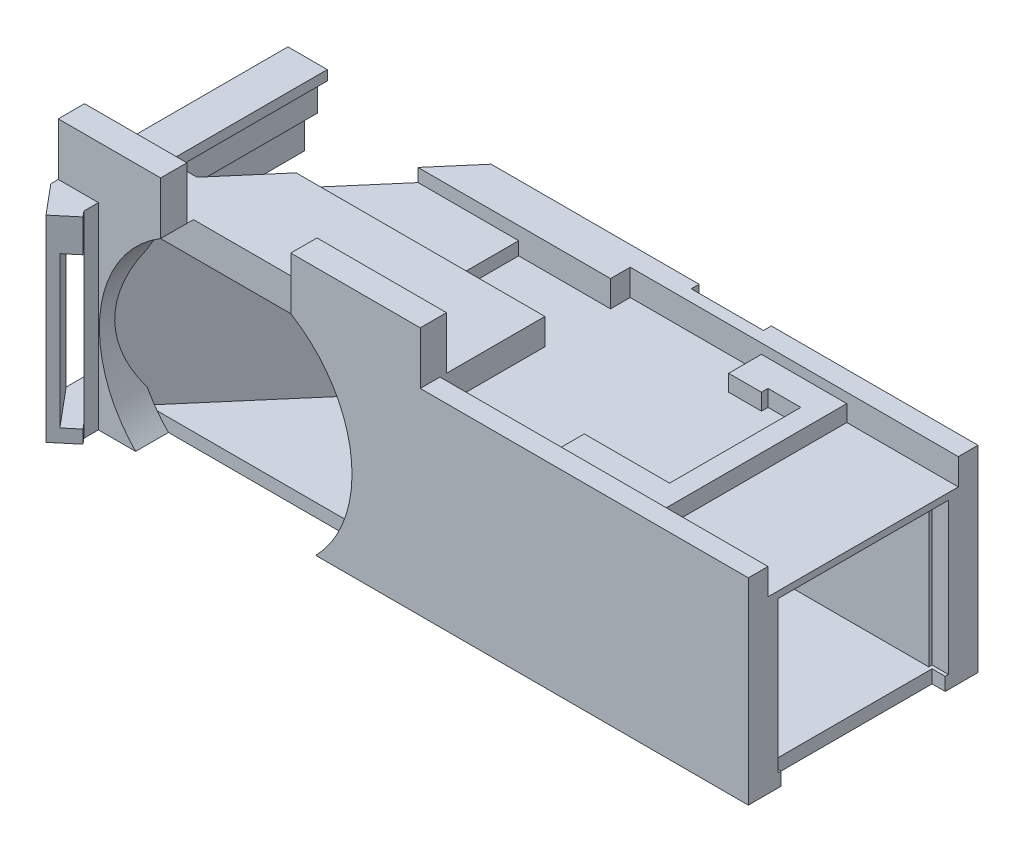
SolidWorks part; units mm, degrees
ref_plane "Front Plane" through (0, 0, 0) normal (0, 0, 1) x (1, 0, 0)
ref_plane "Top Plane" through (0, 0, 0) normal (0, 1, 0) x (1, 0, 0)
ref_plane "Right Plane" through (0, 0, 0) normal (1, 0, 0) x (0, 0, -1)
sketch "Sketch1" plane through (0, 0, 0) normal (0, 1, 0) x (1, 0, 0)
  line L0 (-20.9122, 13.018) -> (-20.9122, 48.018)
  line L1 (-20.9122, 48.018) -> (-75.9122, 48.018)
  line L2 (-75.9122, 48.018) -> (-105.9122, 13.018)
  line L3 (-105.9122, 13.018) -> (-20.9122, 13.018)
  line L4 (-105.9122, 13.018) -> (-65.9122, 13.018)
  line L6 (-110.1779, 11.8828) -> (-110.1779, 48.018)
  line L8 (-105.9122, 48.018) -> (-75.9122, 48.018)
  line L9 (-105.9122, 16.8595) -> (-79.2049, 48.018)
  line L10 (-105.9122, 13.018) -> (-103.3452, 9.9504)
  line L11 (-103.3452, 9.9504) -> (-106.4128, 7.3834)
  line L12 (-106.4128, 7.3834) -> (-110.1779, 11.8828)
  line L13 (-110.1779, 11.8828) -> (-105.9122, 16.8595)
  line L14 (-110.1779, 48.018) -> (-105.9122, 48.018)
  line L15 (-104.1779, 48.018) -> (-104.1779, 18.8828)
  dimension "D2" = 55
  dimension "D3" = 35
  dimension "D6" = 2.5
  dimension "D7" = 6
  dimension "D8" = 4
  dimension "D9" = 4
sketch "Sketch2" plane through (0, 0, 0) normal (0, 1, 0) x (1, 0, 0)
  line L0 (-105.9122, 13.018) -> (-20.9122, 13.018)
  line L1 (-20.9122, 13.018) -> (-20.9122, 48.018)
  line L2 (-20.9122, 48.018) -> (-75.9122, 48.018)
  line L3 (-75.9122, 48.018) -> (-105.9122, 13.018)
sketch "Sketch3" plane through (0, 0, 0) normal (0, 1, 0) x (1, 0, 0)
  line L0 (-106.4128, 7.3834) -> (-110.1779, 11.8828)
  line L1 (-110.1779, 11.8828) -> (-79.2049, 48.018)
  line L2 (-79.2049, 48.018) -> (-75.9122, 48.018)
  line L3 (-75.9122, 48.018) -> (-105.9122, 13.018)
  line L4 (-105.9122, 13.018) -> (-103.3452, 9.9504)
  line L5 (-103.3452, 9.9504) -> (-106.4128, 7.3834)
sketch "Sketch4" plane through (0, 0, 0) normal (0, 1, 0) x (1, 0, 0)
  line L0 (-110.1779, 11.8828) -> (-110.1779, 48.018)
  line L1 (-110.1779, 48.018) -> (-104.1779, 48.018)
  line L2 (-104.1779, 48.018) -> (-104.1779, 18.8828)
  line L3 (-104.1779, 18.8828) -> (-110.1779, 11.8828)
extrude "Boss-Extrude3" add sketch "Sketch2" along normal blind 30
sketch "Sketch6" plane through (-20.9122, 0, 0) normal (1, 0, 0) x (0, 0, -1)
  line L1 (43.018, 2) -> (18.018, 2)
  line L2 (43.018, 2) -> (43.018, 25)
  line L3 (43.018, 25) -> (18.018, 25)
  line L4 (18.018, 2) -> (18.018, 25)
  line L5 (43.018, 2) -> (18.018, 25) construction
  line L6 (43.018, 25) -> (18.018, 2) construction
  line L7 (13.018, 30) -> (13.018, 0) construction
  line L8 (48.018, 30) -> (48.018, 0) construction
  line L9 (13.018, 0) -> (48.018, 0) construction
  line L10 (13.018, 30) -> (48.018, 30) construction
  point P0 (30.518, 13.5)
  dimension "D1" = 5
  dimension "D2" = 5
  dimension "D3" = 2
  dimension "D4" = 5
extrude "Cut-Extrude1" cut sketch "Sketch6" against normal through all
sketch "Sketch7" plane through (-20.9122, 0, 0) normal (1, 0, 0) x (0, 0, -1)
  line L0 (13.018, 30) -> (48.018, 30) construction
  line L1 (18.018, 25) -> (43.018, 25)
  line L2 (18.018, 25) -> (18.018, 30)
  line L3 (18.018, 30) -> (43.018, 30)
  line L4 (43.018, 25) -> (43.018, 30)
extrude "Cut-Extrude2" cut sketch "Sketch7" against normal blind 7.5
sketch "Sketch8" plane through (-20.9122, 0, 0) normal (1, 0, 0) x (0, 0, -1)
  line L0 (13.018, 0) -> (48.018, 0) construction
  line L1 (18.018, 2) -> (43.018, 2)
  line L2 (18.018, 2) -> (18.018, 0)
  line L3 (18.018, 0) -> (43.018, 0)
  line L4 (43.018, 2) -> (43.018, 0)
extrude "Cut-Extrude3" cut sketch "Sketch8" against normal blind 1
sketch "Sketch9" plane through (0, 0, -13.018) normal (0, 0, 1) x (1, 0, 0)
  line L0 (-105.9122, 30) -> (-20.9122, 30) construction
  line L3 (-105.9122, 30) -> (-105.9122, 0) construction
  circle A0 centre (-84.6622, 13.5) radius 19.25
  dimension "D3" = 38.5
  dimension "D1" = 16.5
  dimension "D2" = 21.25
extrude "Cut-Extrude4" cut sketch "Sketch9" against normal blind 5
extrude "Boss-Extrude4" add sketch "Sketch3" along normal blind 30
sketch "Sketch10" plane through (0, 0, -13.018) normal (0, 0, 1) x (1, 0, 0)
  line L0 (-105.9122, 30) -> (-94.5774, 30) construction
  line L1 (-104.0556, 30) -> (-105.9122, 30)
  line L2 (-104.0556, 30) -> (-104.0556, 0)
  line L3 (-104.0556, 0) -> (-105.9122, 0)
  line L4 (-105.9122, 30) -> (-105.9122, 0)
extrude "Boss-Extrude5" add sketch "Sketch10" along normal blind 3
extrude "Boss-Extrude6" add sketch "Sketch4" along normal blind 30
sketch "Sketch11" plane through (-47.4594, 0, -56.7155) normal (0.6418, 0, 0.7669) x (0.7669, 0, -0.6418)
  line L0 (-72.8711, 30) -> (-72.8711, 0) construction
  line L1 (-75.3711, 25) -> (-72.8711, 25)
  line L2 (-75.3711, 25) -> (-75.3711, 2)
  line L3 (-75.3711, 2) -> (-72.8711, 2)
  line L4 (-72.8711, 25) -> (-72.8711, 2)
  line L5 (-76.8711, 30) -> (-72.8711, 30) construction
  line L6 (-76.8711, 0) -> (-70.4058, 0) construction
  dimension "D1" = 2.5
  dimension "D2" = 5
  dimension "D3" = 2
extrude "Cut-Extrude5" cut sketch "Sketch11" against normal through all
sketch "Sketch12" plane through (-104.1779, 0, 0) normal (1, 0, 0) x (0, 0, -1)
  line L0 (48.018, 30) -> (48.018, 0) construction
  line L1 (18.8828, 27.5) -> (48.018, 27.5)
  line L2 (18.8828, 27.5) -> (18.8828, 2.5)
  line L3 (18.8828, 2.5) -> (48.018, 2.5)
  line L4 (48.018, 27.5) -> (48.018, 2.5)
  line L5 (18.8828, 30) -> (18.8828, 0) construction
  line L6 (18.8828, 30) -> (48.018, 30) construction
  dimension "D1" = 25
  dimension "D2" = 2.5
extrude "Cut-Extrude6" cut sketch "Sketch12" against normal blind 3.5
sketch "Sketch13" plane through (-107.6779, 0, 0) normal (1, 0, 0) x (0, 0, -1)
  line L0 (48.018, 27.5) -> (18.8828, 27.5) construction
  line L1 (28.8828, 17.5) -> (48.018, 17.5)
  line L2 (28.8828, 17.5) -> (28.8828, 12.5)
  line L3 (28.8828, 12.5) -> (48.018, 12.5)
  line L4 (48.018, 17.5) -> (48.018, 12.5)
  line L5 (18.8828, 2.5) -> (48.018, 2.5) construction
  line L6 (18.8828, 27.5) -> (18.8828, 2.5) construction
  line L7 (48.018, 2.5) -> (48.018, 27.5) construction
  dimension "D1" = 10
  dimension "D2" = 10
  dimension "D3" = 10
extrude "Cut-Extrude7" cut sketch "Sketch13" against normal through all
sketch "Sketch14" plane through (-107.6779, 0, 0) normal (1, 0, 0) x (0, 0, -1)
  line L0 (48.018, 27.5) -> (18.8828, 27.5) construction
  line L1 (18.8828, 23.5) -> (48.018, 23.5)
  line L2 (18.8828, 23.5) -> (18.8828, 27.5)
  line L3 (18.8828, 27.5) -> (48.018, 27.5)
  line L4 (48.018, 23.5) -> (48.018, 27.5)
  line L5 (48.018, 17.5) -> (48.018, 27.5) construction
  line L6 (18.8828, 27.5) -> (18.8828, 2.5) construction
  point P11 (33.4504, 23.5)
  dimension "D1" = 4
extrude "Boss-Extrude7" add sketch "Sketch14" along normal blind 2
sketch "Sketch16" plane through (-107.6779, 0, 0) normal (1, 0, 0) x (0, 0, -1)
  line L0 (18.8828, 2.5) -> (48.018, 2.5) construction
  line L1 (18.8828, 4) -> (48.018, 4)
  line L2 (18.8828, 4) -> (18.8828, 2.5)
  line L3 (18.8828, 2.5) -> (48.018, 2.5)
  line L4 (48.018, 4) -> (48.018, 2.5)
  line L5 (18.8828, 23.5) -> (18.8828, 2.5) construction
  line L6 (48.018, 2.5) -> (48.018, 12.5) construction
  dimension "D1" = 1.5
extrude "Boss-Extrude8" add sketch "Sketch16" along normal blind 2
sketch "Sketch17" plane through (0, 0, -18.8828) normal (0, 0, -1) x (-1, 0, 0)
  line L0 (104.1779, 27.5) -> (104.1779, 2.5) construction
  line L1 (101.6264, 30) -> (104.1779, 30)
  line L2 (101.6264, 30) -> (101.6264, 0)
  line L3 (101.6264, 0) -> (104.1779, 0)
  line L4 (104.1779, 30) -> (104.1779, 0)
  line L5 (101.6264, 4.4019) -> (101.6264, 2) construction
  line L6 (94.5774, 30) -> (74.7469, 30) construction
  dimension "D1" = 30
extrude "Boss-Extrude9" add sketch "Sketch17" along normal blind 5
sketch "Sketch18" plane through (-104.1779, 0, 0) normal (1, 0, 0) x (0, 0, -1)
  line L1 (48.018, 2.5) -> (18.8828, 2.5)
  line L2 (48.018, 2.5) -> (48.018, 0)
  line L3 (48.018, 0) -> (18.8828, 0)
  line L4 (18.8828, 2.5) -> (18.8828, 0)
extrude "Boss-Extrude10" add sketch "Sketch18" along normal up to surface (24.9731 mm away)
sketch "Sketch19" plane through (-67.4877, 0, -57.8466) normal (0.7593, 0, 0.6508) x (0.6508, 0, -0.7593)
  line L0 (-19.5304, 25) -> (-52.4573, 25) construction
  line L1 (-32.9673, 25) -> (-30.4788, 25)
  line L2 (-32.9673, 25) -> (-32.9673, 2)
  line L3 (-32.9673, 2) -> (-30.4788, 2)
  line L4 (-30.4788, 25) -> (-30.4788, 2)
  line L5 (-52.4573, 2) -> (-19.5304, 2) construction
extrude "Boss-Extrude11" add sketch "Sketch19" along normal blind 2
sketch "Sketch20" plane through (-19.8353, 0, 23.1412) normal (0.6508, 0, -0.7593) x (-0.7593, 0, -0.6508)
  line L1 (88.8865, 25) -> (86.8865, 25)
  line L2 (88.8865, 25) -> (88.8865, 2)
  line L3 (88.8865, 2) -> (86.8865, 2)
  line L4 (86.8865, 25) -> (86.8865, 2)
extrude "Cut-Extrude8" cut sketch "Sketch20" against normal up to surface and the other way up to surface
sketch "Sketch21" plane through (-101.6264, 0, 0) normal (1, 0, 0) x (0, 0, -1)
  line L0 (21.8595, 30) -> (21.8595, 2.5) construction
  line L1 (21.8595, 30) -> (23.8828, 30)
  line L2 (21.8595, 30) -> (21.8595, 2.5)
  line L3 (21.8595, 2.5) -> (23.8828, 2.5)
  line L4 (23.8828, 30) -> (23.8828, 2.5)
  line L5 (23.8828, 30) -> (21.8595, 30) construction
extrude "Boss-Extrude12" add sketch "Sketch21" along normal up to surface (1.7342 mm away)
sketch "Sketch22" plane through (-20.9122, 0, 0) normal (1, 0, 0) x (0, 0, -1)
  line L1 (13.018, 30) -> (48.018, 30)
  line L2 (13.018, 30) -> (13.018, 0)
  line L3 (13.018, 0) -> (48.018, 0)
  line L4 (48.018, 30) -> (48.018, 0)
extrude "Boss-Extrude13" add sketch "Sketch22" along normal blind 15.9 and the other way up to vertex (7.5 mm away)
sketch "Sketch23" plane through (-28.4122, 0, 0) normal (-1, 0, 0) x (0, 0, 1)
  line L0 (-18.018, 25) -> (-43.018, 25) construction
  line L1 (-43.018, 25) -> (-18.018, 25)
  line L2 (-43.018, 25) -> (-43.018, 2)
  line L3 (-43.018, 2) -> (-18.018, 2)
  line L4 (-18.018, 25) -> (-18.018, 2)
extrude "Cut-Extrude9" cut sketch "Sketch23" against normal through all
sketch "Sketch24" plane through (-5.0122, 0, 0) normal (1, 0, 0) x (0, 0, -1)
  line L0 (48.018, 30) -> (13.018, 30) construction
  line L1 (43.018, 30) -> (18.018, 30)
  line L2 (43.018, 30) -> (43.018, 25)
  line L3 (43.018, 25) -> (18.018, 25)
  line L4 (18.018, 30) -> (18.018, 25)
extrude "Cut-Extrude10" cut sketch "Sketch24" against normal blind 2
sketch "Sketch25" plane through (0, 30, 0) normal (0, 1, 0) x (1, 0, 0)
  line L1 (-5.0122, 16.018) -> (-55.0122, 16.018)
  line L2 (-5.0122, 16.018) -> (-5.0122, 45.018)
  line L3 (-5.0122, 45.018) -> (-55.0122, 45.018)
  line L4 (-55.0122, 16.018) -> (-55.0122, 45.018)
  line L5 (-74.7469, 13.018) -> (-5.0122, 13.018) construction
  line L6 (-5.0122, 48.018) -> (-79.2049, 48.018) construction
  line L7 (-5.0122, 18.018) -> (-5.0122, 13.018) construction
  dimension "D1" = 3
  dimension "D2" = 3
  dimension "D3" = 50
extrude "Cut-Extrude11" cut sketch "Sketch25" against normal blind 4
sketch "Sketch26" plane through (0, 26, 0) normal (0, 1, 0) x (1, 0, 0)
  line L0 (-55.0122, 16.018) -> (-5.0122, 16.018) construction
  line L1 (-22.0122, 16.018) -> (-25.0122, 16.018)
  line L2 (-22.0122, 16.018) -> (-22.0122, 45.018)
  line L3 (-22.0122, 45.018) -> (-25.0122, 45.018)
  line L4 (-25.0122, 16.018) -> (-25.0122, 45.018)
  line L5 (-5.0122, 45.018) -> (-55.0122, 45.018) construction
  line L6 (-5.0122, 16.018) -> (-5.0122, 18.018) construction
  point P10 (-5.0122, 17.018)
  dimension "D1" = 17
  dimension "D2" = 20
extrude "Boss-Extrude14" add sketch "Sketch26" along normal blind 2.5
sketch "Sketch27" plane through (0, 26, 0) normal (0, 1, 0) x (1, 0, 0)
  line L0 (-25.0122, 45.018) -> (-55.0122, 45.018) construction
  line L1 (-35.0122, 40.018) -> (-30.0122, 40.018)
  line L2 (-35.0122, 40.018) -> (-35.0122, 45.018)
  line L3 (-35.0122, 45.018) -> (-30.0122, 45.018)
  line L4 (-30.0122, 40.018) -> (-30.0122, 45.018)
  line L5 (-5.0122, 43.018) -> (-5.0122, 45.018) construction
  dimension "D1" = 5
  dimension "D2" = 25
  dimension "D3" = 30
extrude "Boss-Extrude15" add sketch "Sketch27" along normal blind 2.5
sketch "Sketch28" plane through (-30.0122, 0, 0) normal (1, 0, 0) x (0, 0, -1)
  line L0 (40.018, 28.5) -> (45.018, 28.5) construction
  line L1 (45.018, 26) -> (41.018, 26)
  line L2 (45.018, 26) -> (45.018, 28.5)
  line L3 (45.018, 28.5) -> (41.018, 28.5)
  line L4 (41.018, 26) -> (41.018, 28.5)
  line L5 (40.018, 26) -> (45.018, 26) construction
  line L6 (45.018, 28.5) -> (45.018, 26) construction
  dimension "D1" = 4
extrude "Boss-Extrude16" add sketch "Sketch28" along normal up to next
sketch "Sketch29" plane through (0, 26, 0) normal (0, 1, 0) x (1, 0, 0)
  line L0 (-5.0122, 16.018) -> (-5.0122, 18.018) construction
  line L1 (-38.0122, 21.018) -> (-25.0122, 21.018)
  line L2 (-38.0122, 21.018) -> (-38.0122, 16.018)
  line L3 (-38.0122, 16.018) -> (-25.0122, 16.018)
  line L4 (-25.0122, 21.018) -> (-25.0122, 16.018)
  dimension "D1" = 5
  dimension "D2" = 33
extrude "Boss-Extrude17" add sketch "Sketch29" along normal blind 2.5
sketch "Sketch30" plane through (-55.0122, 0, 0) normal (1, 0, 0) x (0, 0, -1)
  line L0 (45.018, 30) -> (16.018, 30) construction
  line L1 (42.018, 30) -> (32.018, 30)
  line L2 (42.018, 30) -> (42.018, 26)
  line L3 (42.018, 26) -> (32.018, 26)
  line L4 (32.018, 30) -> (32.018, 26)
  line L5 (45.018, 26) -> (16.018, 26) construction
  line L6 (45.018, 26) -> (45.018, 30) construction
  dimension "D1" = 3
  dimension "D2" = 10
extrude "Cut-Extrude12" cut sketch "Sketch30" against normal blind 14
sketch "Sketch31" plane through (-69.0122, 0, 0) normal (1, 0, 0) x (0, 0, -1)
  line L0 (42.018, 30) -> (32.018, 30) construction
  line L1 (32.018, 30) -> (42.018, 30)
  line L2 (32.018, 30) -> (32.018, 28)
  line L3 (32.018, 28) -> (42.018, 28)
  line L4 (42.018, 30) -> (42.018, 28)
  line L5 (42.018, 26) -> (42.018, 30) construction
extrude "Cut-Extrude13" cut sketch "Sketch31" against normal up to next
sketch "Sketch32" plane through (0, 26, 0) normal (0, 1, 0) x (1, 0, 0)
  line L1 (-7.0122, 18.018) -> (-5.0122, 18.018)
  line L2 (-7.0122, 18.018) -> (-7.0122, 43.018)
  line L3 (-7.0122, 43.018) -> (-5.0122, 43.018)
  line L4 (-5.0122, 18.018) -> (-5.0122, 43.018)
extrude "Cut-Extrude14" cut sketch "Sketch32" against normal through all
sketch "Sketch33" plane through (0, 30, 0) normal (0, 1, 0) x (1, 0, 0)
  line L0 (-74.7469, 13.018) -> (-5.0122, 13.018) construction
  line L1 (-55.0122, 13.018) -> (-74.7469, 13.018)
  line L2 (-55.0122, 13.018) -> (-55.0122, 17.018)
  line L3 (-55.0122, 17.018) -> (-74.7469, 17.018)
  line L4 (-74.7469, 13.018) -> (-74.7469, 17.018)
  line L5 (-74.7469, 13.018) -> (-74.7469, 18.018) construction
  dimension "D1" = 4
extrude "Boss-Extrude18" add sketch "Sketch33" along normal blind 8
sketch "Sketch34" plane through (0, 30, 0) normal (0, 1, 0) x (1, 0, 0)
  line L0 (-110.1779, 48.018) -> (-110.1779, 11.8828) construction
  line L1 (-94.5774, 13.018) -> (-110.1779, 13.018)
  line L2 (-94.5774, 13.018) -> (-94.5774, 17.018)
  line L3 (-94.5774, 17.018) -> (-110.1779, 17.018)
  line L4 (-110.1779, 13.018) -> (-110.1779, 17.018)
  dimension "D1" = 4
extrude "Boss-Extrude19" add sketch "Sketch34" along normal blind 8
sketch "Sketch35" plane through (-5.0122, 0, 0) normal (1, 0, 0) x (0, 0, -1)
  line L2 (18.018, 0) -> (18.018, 26) construction
  line L3 (17.518, 25) -> (43.518, 25)
  line L4 (17.518, 25) -> (17.518, 2)
  line L5 (17.518, 2) -> (43.518, 2)
  line L6 (43.518, 25) -> (43.518, 2)
  line L7 (43.018, 26) -> (43.018, 0) construction
  line L8 (18.018, 25) -> (43.018, 25) construction
  line L9 (18.018, 2) -> (43.018, 2) construction
  dimension "D1" = 0.5
  dimension "D2" = 0.5
extrude "Cut-Extrude15" cut sketch "Sketch35" against normal blind 2.5 contours L4 L5 L6 L3
sketch "Sketch36" plane through (-7.0122, 0, 0) normal (1, 0, 0) x (0, 0, -1)
  line L0 (43.018, 25) -> (43.018, 26) construction
  line L1 (18.018, 26) -> (43.018, 26)
  line L2 (18.018, 26) -> (18.018, 25)
  line L3 (18.018, 25) -> (43.018, 25)
  line L4 (43.018, 26) -> (43.018, 25)
  line L5 (18.018, 25) -> (43.018, 25) construction
extrude "Boss-Extrude20" add sketch "Sketch36" along normal blind 2
sketch "Sketch39" plane through (0, 0, -48.018) normal (0, 0, -1) x (-1, 0, 0)
  line L2 (104.1779, 27.5) -> (105.6779, 27.5)
  line L4 (104.1779, 27.5) -> (104.1779, 28.5)
  line L5 (104.1779, 28.5) -> (105.6779, 28.5)
  line L7 (105.6779, 27.5) -> (105.6779, 28.5)
  dimension "D1" = 1
extrude "Cut-Extrude16" cut sketch "Sketch39" against normal up to surface (29.1352 mm away) up to face at (-105.8029, 14.375, -18.8828)
sketch "Sketch42" plane through (0, 0, -48.018) normal (0, 0, -1) x (-1, 0, 0)
  line L0 (5.0122, 30) -> (79.2049, 30) construction
  line L1 (36.5122, 30) -> (47.5122, 30)
  line L2 (36.5122, 30) -> (36.5122, 28)
  line L3 (36.5122, 28) -> (47.5122, 28)
  line L4 (47.5122, 30) -> (47.5122, 28)
  line L5 (5.0122, 0) -> (5.0122, 30) construction
  dimension "D1" = 42.5
  dimension "D2" = 31.5
  dimension "D3" = 2
extrude "Cut-Extrude17" cut sketch "Sketch42" against normal blind 1.2
